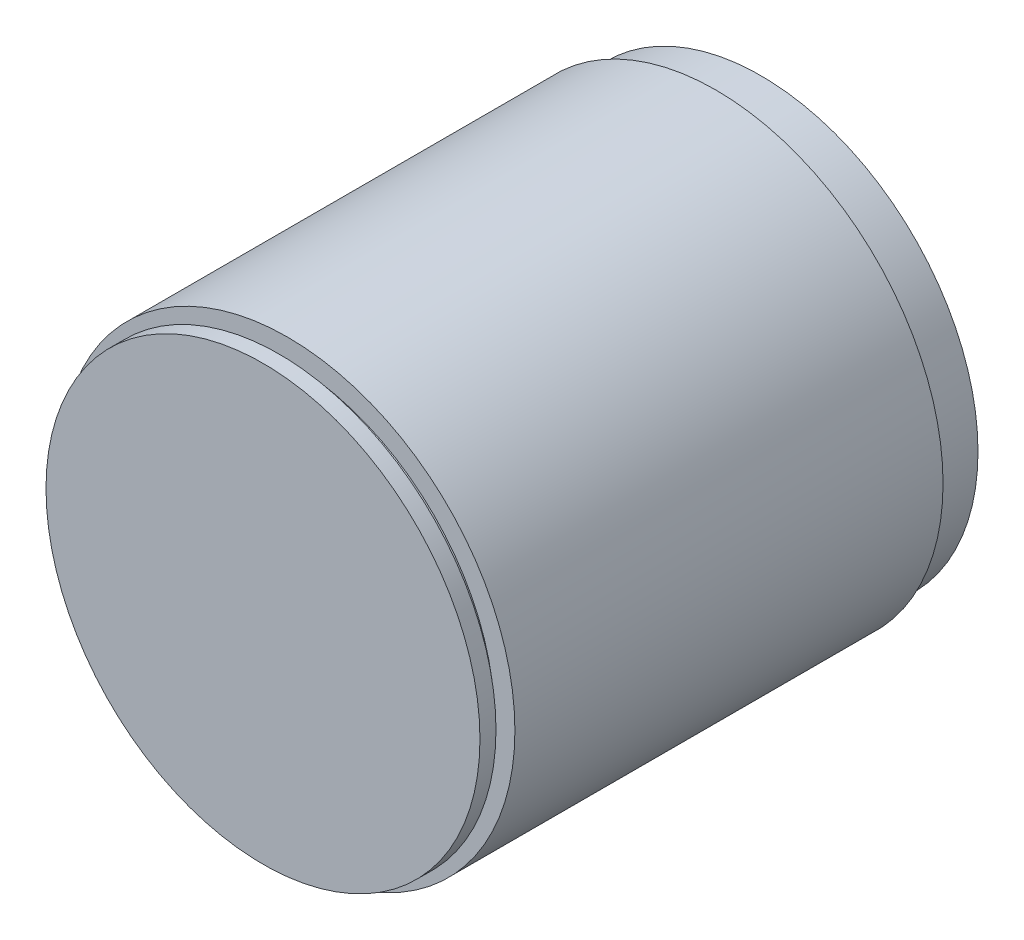
SolidWorks part; units mm, degrees
ref_plane "Alzado" through (0, 0, 0) normal (0, 0, 1) x (1, 0, 0)
ref_plane "Planta" through (0, 0, 0) normal (0, 1, 0) x (1, 0, 0)
ref_plane "Vista lateral" through (0, 0, 0) normal (1, 0, 0) x (0, 0, -1)
sketch "Croquis1" plane through (0, 0, 0) normal (0, 1, 0) x (1, 0, 0)
  line L0 (0, 76.1183) -> (0, -88.1243) construction
  line L1 (101.8112, -88.1243) -> (173.3672, -88.1243)
  line L2 (173.3672, -88.1243) -> (173.3672, -82.8417)
  line L3 (173.3672, -82.8417) -> (170.0055, -82.8417)
  line L4 (170.0055, -82.8417) -> (170.0055, -79.9602)
  line L5 (170.0055, -79.9602) -> (176.7289, -79.9602)
  line L6 (176.7289, -79.9602) -> (176.7289, 61.2308)
  line L7 (176.7289, 61.2308) -> (173.3672, 61.2308)
  line L8 (173.3672, 61.2308) -> (173.3672, 67.9542)
  line L9 (173.3672, 67.9542) -> (173.3672, 76.1183)
  line L10 (173.3672, 76.1183) -> (101.8112, 76.1183)
  line L11 (101.8112, 76.1183) -> (101.8112, -88.1243)
revolve "Revolución1" add sketch "Croquis1" angle 360 about L11
